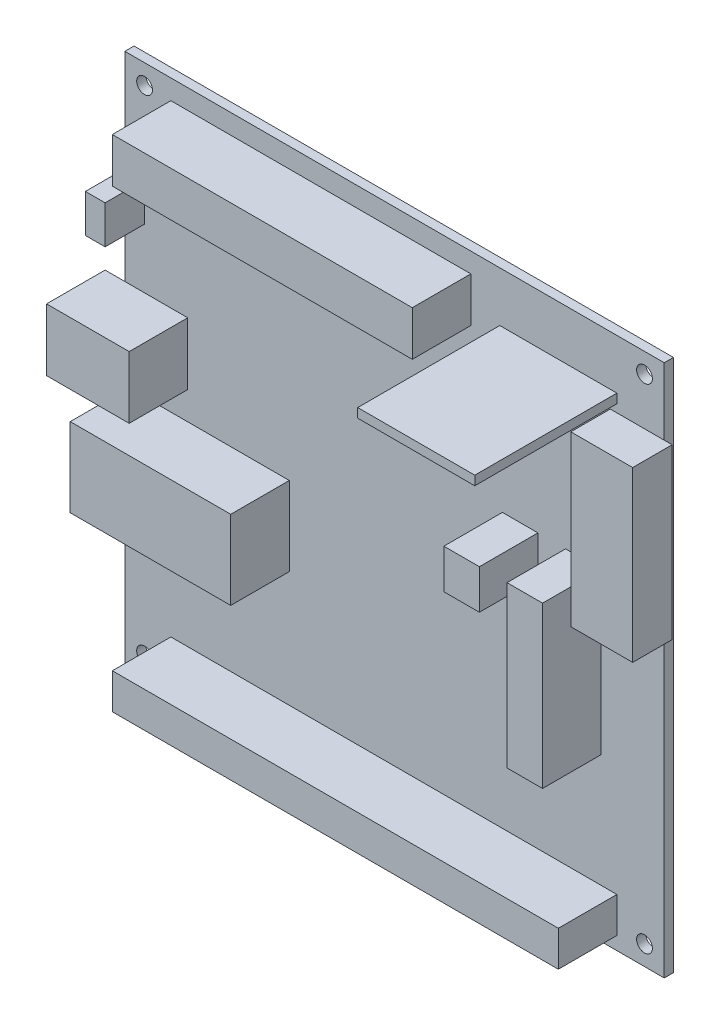
SolidWorks part; units mm, degrees
ref_plane "Front Plane" through (0, 0, 0) normal (0, 0, 1) x (1, 0, 0)
ref_plane "Top Plane" through (0, 0, 0) normal (0, 1, 0) x (1, 0, 0)
ref_plane "Right Plane" through (0, 0, 0) normal (1, 0, 0) x (0, 0, -1)
sketch "Sketch1" plane through (0, 0, 0) normal (0, 0, 1) x (1, 0, 0)
  line L0 (-52.07, -51.435) -> (52.07, 51.435) construction
  line L1 (-52.07, 51.435) -> (52.07, 51.435)
  line L2 (-52.07, 51.435) -> (-52.07, -51.435)
  line L3 (-52.07, -51.435) -> (52.07, -51.435)
  line L4 (52.07, 51.435) -> (52.07, -51.435)
  line L5 (-48.26, 47.625) -> (48.26, -47.625) construction
  circle A0 centre (-48.26, 47.625) radius 1.524
  circle A1 centre (48.26, 47.625) radius 1.524
  circle A2 centre (48.26, -47.625) radius 1.524
  circle A3 centre (-48.26, -47.625) radius 1.524
  dimension "D5" = 3.048
  dimension "D1" = 96.52
  dimension "D2" = 95.25
  dimension "D3" = 102.87
  dimension "D4" = 104.14
extrude "Boss-Extrude1" add sketch "Sketch1" along normal blind 1.778
sketch "Sketch2" plane through (0, 0, 1.778) normal (0, 0, 1) x (1, 0, 0)
  line L0 (52.07, 51.435) -> (-52.07, 51.435) construction
  line L1 (-43.18, 47.625) -> (14.732, 47.625)
  line L2 (-43.18, 47.625) -> (-43.18, 38.989)
  line L3 (-43.18, 38.989) -> (14.732, 38.989)
  line L4 (14.732, 47.625) -> (14.732, 38.989)
  line L5 (-55.88, 12.955) -> (-39.9288, 12.955)
  line L6 (-55.88, 12.955) -> (-55.88, 0.955)
  line L7 (-55.88, 0.955) -> (-39.9288, 0.955)
  line L8 (-39.9288, 12.955) -> (-39.9288, 0.955)
  line L9 (-51.308, -4.445) -> (-20.32, -4.445)
  line L10 (-51.308, -4.445) -> (-51.308, -19.685)
  line L11 (-51.308, -19.685) -> (-20.32, -19.685)
  line L12 (-20.32, -4.445) -> (-20.32, -19.685)
  line L13 (-43.18, -42.037) -> (42.926, -42.037)
  line L14 (-43.18, -42.037) -> (-43.18, -48.895)
  line L15 (-43.18, -48.895) -> (42.926, -48.895)
  line L16 (42.926, -42.037) -> (42.926, -48.895)
  line L17 (33.02, 10.795) -> (39.878, 10.795)
  line L18 (33.02, 10.795) -> (33.02, -20.193)
  line L19 (33.02, -20.193) -> (39.878, -20.193)
  line L20 (39.878, 10.795) -> (39.878, -20.193)
  line L21 (20.828, 10.795) -> (27.686, 10.795)
  line L22 (20.828, 10.795) -> (20.828, 3.175)
  line L23 (20.828, 3.175) -> (27.686, 3.175)
  line L24 (27.686, 10.795) -> (27.686, 3.175)
  line L25 (-52.07, 51.435) -> (-52.07, -51.435) construction
  line L26 (-52.07, -51.435) -> (52.07, -51.435) construction
  line L27 (52.07, -51.435) -> (52.07, 51.435) construction
  dimension "D1" = 3.81
  dimension "D2" = 8.636
  dimension "D3" = 8.89
  dimension "D4" = 57.912
  dimension "D5" = 52.39
  dimension "D6" = 64.39
  dimension "D7" = 3.81
  dimension "D8" = 15.9512
  dimension "D9" = 46.99
  dimension "D10" = 31.75
  dimension "D11" = 30.988
  dimension "D12" = 15.24
  dimension "D13" = 86.106
  dimension "D14" = 9.398
  dimension "D15" = 6.858
  dimension "D16" = 8.89
  dimension "D17" = 62.23
  dimension "D18" = 6.858
  dimension "D19" = 19.05
  dimension "D20" = 30.988
  dimension "D21" = 7.62
  dimension "D22" = 5.334
extrude "Boss-Extrude2" add sketch "Sketch2" along normal blind 11.303
sketch "Sketch3" plane through (0, 0, 1.778) normal (0, 0, 1) x (1, 0, 0)
  line L0 (-52.07, 51.435) -> (-52.07, 12.955) construction
  line L1 (41.656, 38.485) -> (53.594, 38.485)
  line L2 (41.656, 38.485) -> (41.656, 5.905)
  line L3 (41.656, 5.905) -> (53.594, 5.905)
  line L4 (53.594, 38.485) -> (53.594, 5.905)
  line L5 (-52.07, 31.818) -> (-48.26, 31.818)
  line L6 (-52.07, 31.818) -> (-52.07, 24.452)
  line L7 (-52.07, 24.452) -> (-48.26, 24.452)
  line L8 (-48.26, 31.818) -> (-48.26, 24.452)
  line L10 (52.07, -51.435) -> (52.07, 51.435) construction
  line L11 (-52.07, 28.135) -> (-48.26, 28.135) construction
  line L12 (-52.07, -51.435) -> (52.07, -51.435) construction
  dimension "D1" = 79.57
  dimension "D2" = 7.366
  dimension "D3" = 3.81
  dimension "D4" = 11.938
  dimension "D5" = 10.414
  dimension "D6" = 57.34
  dimension "D7" = 89.92
extrude "Boss-Extrude3" add sketch "Sketch3" along normal blind 7.62
sketch "Sketch4" plane through (-52.07, 0, 0) normal (-1, 0, 0) x (0, 0, 1)
  line L0 (0, 51.435) -> (0, -51.435) construction
  line L1 (1.778, 51.435) -> (0, 51.435) construction
  line L2 (1.778, -51.435) -> (0, -51.435) construction
  circle A0 centre (6.096, 28.135) radius 1.7463
  point P4 (0.889, 51.435)
  dimension "D3" = 3.4925
  dimension "D1" = 6.096
  dimension "D2" = 79.57
extrude "Boss-Extrude4" add sketch "Sketch4" along normal blind 0.762
sketch "Sketch5" plane through (0, 0, 1.778) normal (0, 0, 1) x (1, 0, 0)
  line L0 (52.07, 51.435) -> (-52.07, 51.435) construction
  line L1 (20.32, 41.783) -> (42.926, 41.783)
  line L2 (20.32, 41.783) -> (20.32, 40.005)
  line L3 (20.32, 40.005) -> (42.926, 40.005)
  line L4 (42.926, 41.783) -> (42.926, 40.005)
  line L5 (52.07, 38.485) -> (52.07, 51.435) construction
  dimension "D1" = 11.43
  dimension "D2" = 1.778
  dimension "D3" = 31.75
  dimension "D4" = 22.606
extrude "Boss-Extrude5" add sketch "Sketch5" along normal blind 27.432
